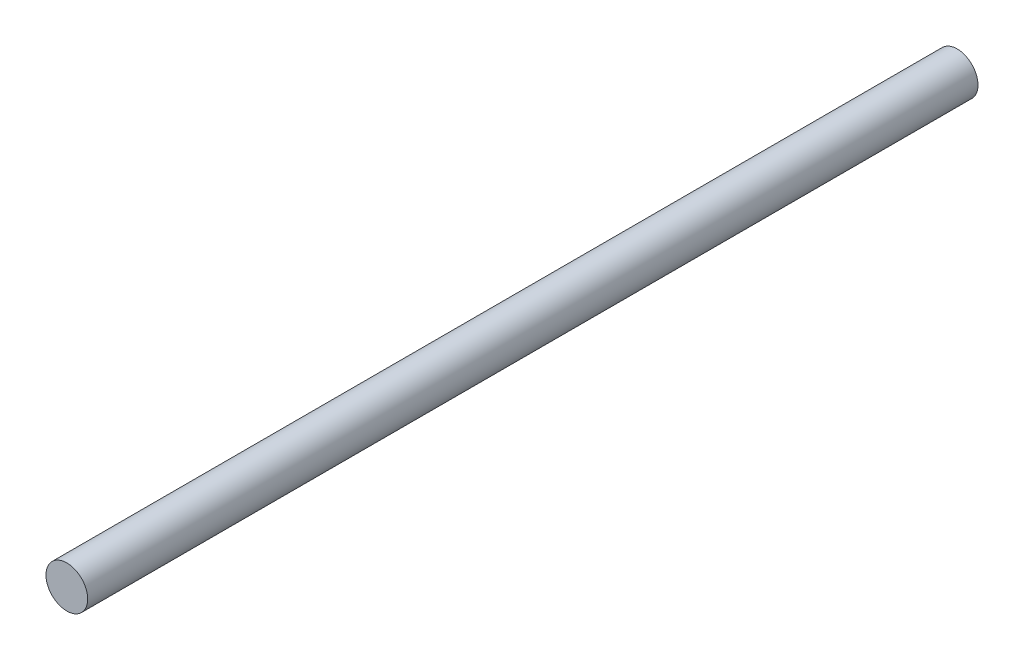
SolidWorks part; units mm, degrees
ref_plane "Front Plane" through (0, 0, 0) normal (0, 0, 1) x (1, 0, 0)
ref_plane "Top Plane" through (0, 0, 0) normal (0, 1, 0) x (1, 0, 0)
ref_plane "Right Plane" through (0, 0, 0) normal (1, 0, 0) x (0, 0, -1)
sketch "Sketch1" plane through (0, 0, 0) normal (0, 0, 1) x (1, 0, 0)
  circle A0 centre (0, 0) radius 2.3813
  dimension "D1" = 4.7625
extrude "Boss-Extrude1" add sketch "Sketch1" along normal blind 101.6
sketch "Sketch2" plane through (0, 0, 0) normal (0, 0, -1) x (-1, 0, 0)
  circle A0 centre (0, 0) radius 1.5875
  circle A1 centre (0, 0) radius 2.3813
  dimension "D1" = 3.175
extrude "Cut-Extrude1" [suppressed] cut sketch "Sketch2" against normal blind 12.7
sketch "Sketch3" plane through (0, 0, 101.6) normal (0, 0, 1) x (1, 0, 0)
  circle A0 centre (0, 0) radius 1.5875
  circle A1 centre (0, 0) radius 2.3813
  dimension "D1" = 3.175
extrude "Cut-Extrude2" [suppressed] cut sketch "Sketch3" against normal blind 12.7
